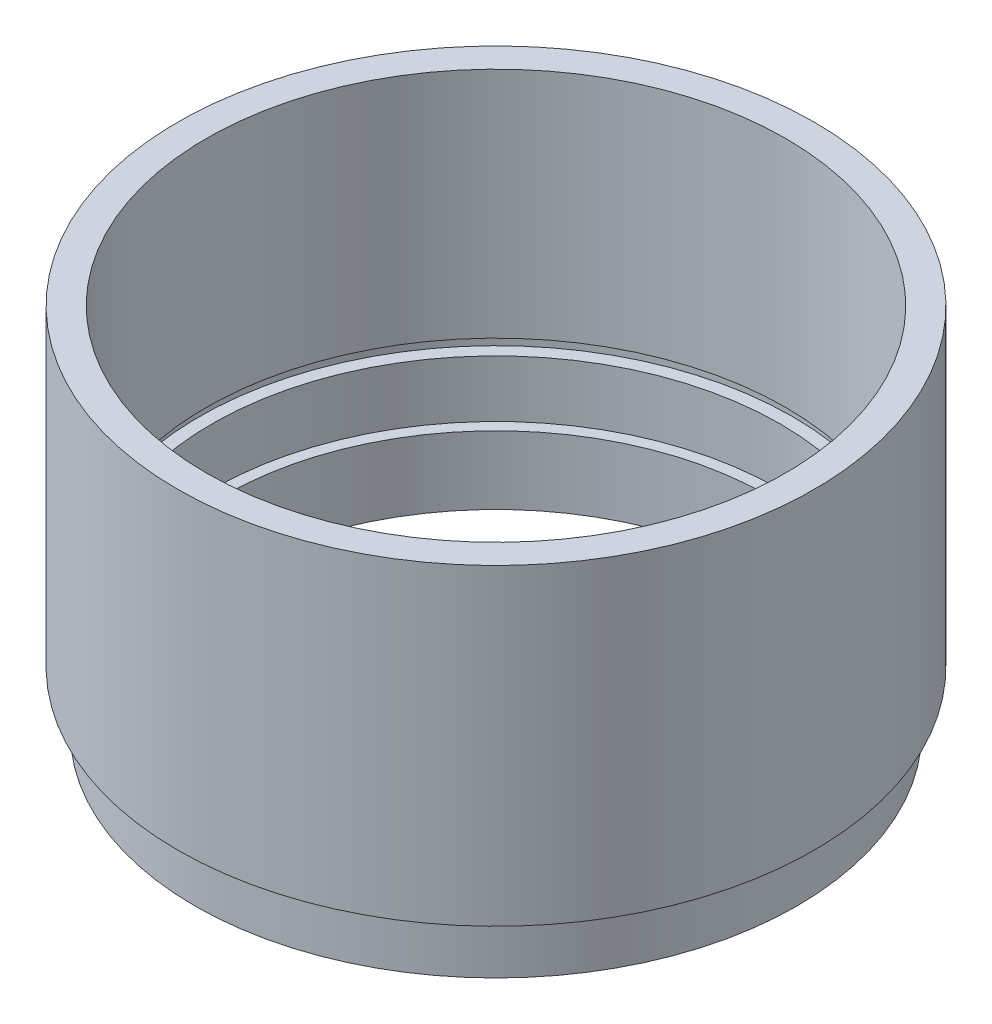
SolidWorks part; units mm, degrees
ref_plane "前视基准面" through (0, 0, 0) normal (0, 0, 1) x (1, 0, 0)
ref_plane "上视基准面" through (0, 0, 0) normal (0, 1, 0) x (1, 0, 0)
ref_plane "右视基准面" through (0, 0, 0) normal (1, 0, 0) x (0, 0, -1)
sketch "草图1" plane through (0, 0, 0) normal (0, 0, 1) x (1, 0, 0)
  line L0 (0, 0) -> (0, 21.8535) construction
  line L1 (24, 0) -> (26.5, 0)
  line L2 (26.5, 0) -> (26.5, 4)
  line L3 (26.5, 4) -> (25.5, 4)
  line L4 (25.5, 4) -> (25.5, 5)
  line L5 (25.5, 5) -> (28, 5)
  line L6 (28, 5) -> (28, 32.5)
  line L7 (28, 32.5) -> (25.5, 32.5)
  line L8 (25.5, 32.5) -> (25.5, 12)
  line L9 (25.5, 12) -> (26.1, 12)
  line L10 (26.1, 12) -> (26.1, 11)
  line L11 (26.1, 11) -> (25, 11)
  line L12 (25, 11) -> (25, 6)
  line L13 (25, 6) -> (24, 6)
  line L14 (24, 0) -> (24, 6)
  dimension "D1" = 32.5
  dimension "D2" = 28
  dimension "D3" = 25.5
  dimension "D4" = 25
  dimension "D5" = 1
  dimension "D6" = 5
  dimension "D7" = 24
  dimension "D8" = 26.5
  dimension "D9" = 1
  dimension "D10" = 5
  dimension "D11" = 6
  dimension "D12" = 26.1
  dimension "D13" = 25.5
revolve "旋转1" add sketch "草图1" angle 360 about L0
cosmetic thread "装饰螺纹线11" parameters "D2"=52
cosmetic thread "装饰螺纹线12" parameters "D2"=52
